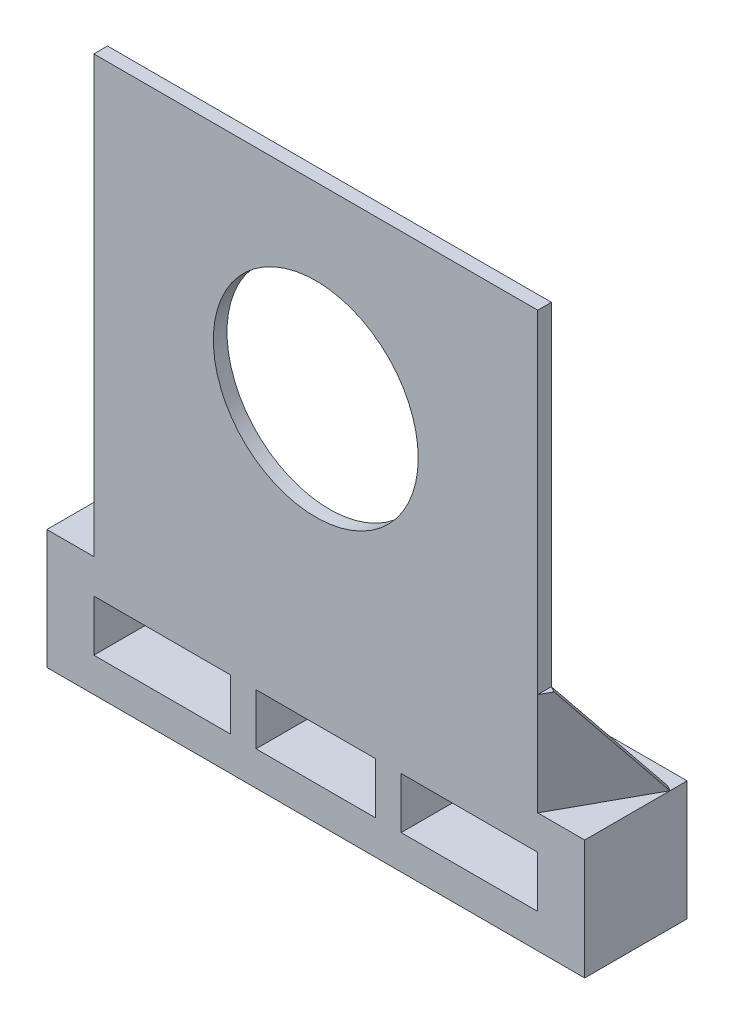
SolidWorks part; units mm, degrees
ref_plane "Front Plane" through (0, 0, 0) normal (0, 0, 1) x (1, 0, 0)
ref_plane "Top Plane" through (0, 0, 0) normal (0, 1, 0) x (1, 0, 0)
ref_plane "Right Plane" through (0, 0, 0) normal (1, 0, 0) x (0, 0, -1)
sketch "Sketch1" plane through (0, 0, 0) normal (0, 0, 1) x (1, 0, 0)
  line L1 (-130, -127.5) -> (130, -127.5)
  line L2 (-130, -127.5) -> (-130, 127.5)
  line L3 (-130, 127.5) -> (130, 127.5)
  line L4 (130, -127.5) -> (130, 127.5)
  line L5 (-130, -127.5) -> (130, 127.5) construction
  line L6 (-130, 127.5) -> (130, -127.5) construction
  circle A0 centre (0, 17.5) radius 60
  point P0 (0, 0)
  point P8 (0, 0)
  dimension "D3" = 120
  dimension "D1" = 255
  dimension "D2" = 260
  dimension "D4" = 110
extrude "Boss-Extrude1" add sketch "Sketch1" against normal blind 8
sketch "Sketch2" plane through (0, 0, 0) normal (0, 0, 1) x (1, 0, 0)
  line L0 (-130, -127.5) -> (130, -127.5) construction
  line L1 (157.5, -197.5) -> (-157.5, -197.5)
  line L2 (157.5, -197.5) -> (157.5, -127.5)
  line L3 (157.5, -127.5) -> (-157.5, -127.5)
  line L4 (-157.5, -197.5) -> (-157.5, -127.5)
  line L5 (157.5, -197.5) -> (-157.5, -127.5) construction
  line L6 (157.5, -127.5) -> (-157.5, -197.5) construction
  line L8 (-35, -177.5) -> (35, -177.5)
  line L9 (-35, -177.5) -> (-35, -147.5)
  line L10 (-35, -147.5) -> (35, -147.5)
  line L11 (35, -177.5) -> (35, -147.5)
  line L12 (-35, -177.5) -> (35, -147.5) construction
  line L13 (-35, -147.5) -> (35, -177.5) construction
  line L18 (50, -177.5) -> (130, -177.5)
  line L19 (50, -177.5) -> (50, -147.5)
  line L20 (-130.1794, -177.5) -> (-50, -177.5)
  line L21 (-130.1794, -177.5) -> (-130.1794, -147.5)
  line L22 (-130.1794, -147.5) -> (-50, -147.5)
  line L23 (-50, -177.5) -> (-50, -147.5)
  line L24 (-130.1794, -177.5) -> (-50, -147.5) construction
  line L25 (-130.1794, -147.5) -> (-50, -177.5) construction
  line L26 (50, -147.5) -> (130, -147.5)
  line L27 (130, -177.5) -> (130, -147.5)
  line L28 (50, -177.5) -> (130, -147.5) construction
  line L29 (50, -147.5) -> (130, -177.5) construction
  point P0 (0, -162.5)
  point P8 (0, -162.5)
  point P13 (90, -162.5)
  point P18 (-90.0897, -162.5)
  dimension "D1" = 315
  dimension "D2" = 70
  dimension "D3" = 70
  dimension "D4" = 80
  dimension "D5" = 30
  dimension "D6" = 15
  dimension "D7" = 30
  dimension "D8" = 15
extrude "Boss-Extrude2" add sketch "Sketch2" against normal blind 60
sketch "Sketch3" plane through (0, -127.5, 0) normal (0, 1, 0) x (1, 0, 0)
  line L0 (130, 0) -> (157.5, 50)
  line L1 (157.5, 60) -> (157.5, 0) construction
  line L2 (130, 8) -> (154.1219, 51.858)
  line L3 (154.1219, 51.858) -> (157.5, 50)
  line L8 (-130, 0) -> (130, 0)
  line L9 (130, 0) -> (130, 8)
  line L10 (130, 8) -> (-130, 8)
  line L11 (-130, 8) -> (-130, 0)
  line L13 (130, 0) -> (130, 8)
  dimension "D1" = 50
  dimension "D2" = 0
sketch "Sketch4" plane through (0, -127.5, 0) normal (0, 1, 0) x (1, 0, 0)
extrude "Boss-Extrude3" add sketch "Sketch3" along normal blind 60
mirror "Mirror1" about plane through (0, 0, 0) normal (1, 0, 0) of bodies 103
sketch "Sketch6" plane through (99.8081, 0, 54.8944) normal (0.8762, 0, 0.4819) x (0.4819, 0, -0.8762)
  line L0 (69.6592, -67.5) -> (119.713, -127.5)
  line L1 (119.713, -127.5) -> (119.713, -67.5)
  line L2 (119.713, -67.5) -> (69.6592, -67.5)
extrude "Cut-Extrude2" cut sketch "Sketch6" against normal through all
sketch "Sketch7" plane through (-99.8081, 0, 54.8944) normal (-0.8762, 0, 0.4819) x (0.4819, 0, 0.8762)
  line L0 (-69.6592, -67.5) -> (-119.713, -127.5)
  line L1 (-119.713, -127.5) -> (-119.713, -67.5)
  line L2 (-119.713, -67.5) -> (-69.6592, -67.5)
extrude "Cut-Extrude3" cut sketch "Sketch7" against normal through all
